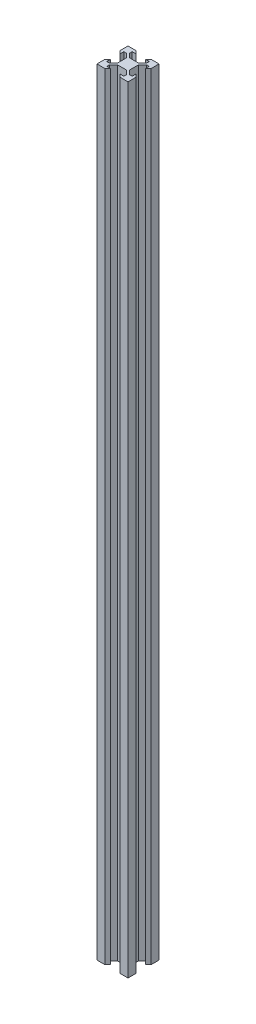
SolidWorks part; units mm, degrees
ref_plane "Front Plane" through (0, 0, 0) normal (0, 0, 1) x (1, 0, 0)
ref_plane "Top Plane" through (0, 0, 0) normal (0, 1, 0) x (1, 0, 0)
ref_plane "Right Plane" through (0, 0, 0) normal (1, 0, 0) x (0, 0, -1)
sketch "Sketch1" plane through (0, 0, 0) normal (0, 1, 0) x (1, 0, 0)
  line L0 (0, 93.8825) -> (0, -83.9719) construction
  line L1 (2.84, -3.9007) -> (-2.84, -3.9007)
  line L2 (3.9007, -2.84) -> (3.9007, 2.84)
  line L3 (2.84, 3.9007) -> (-2.84, 3.9007)
  line L4 (-3.9007, -2.84) -> (-3.9007, 2.84)
  line L7 (-194.997, 0) -> (154.5512, 0) construction
  line L8 (-2.84, -3.9007) -> (-5.4993, -6.56)
  line L9 (-5.4993, -6.56) -> (-5.4993, -8.2)
  line L10 (-5.4993, -8.2) -> (-3.1, -8.2)
  line L11 (-3.1, -8.2) -> (-4.9, -10)
  line L12 (-4.9, -10) -> (-10, -10)
  line L13 (-3.9007, -2.84) -> (-6.56, -5.4993)
  line L14 (-6.56, -5.4993) -> (-8.2, -5.4993)
  line L15 (-8.2, -5.4993) -> (-8.2, -3.1)
  line L16 (-8.2, -3.1) -> (-10, -4.9)
  line L17 (-10, -4.9) -> (-10, -10)
  line L18 (10, -4.9) -> (10, -10)
  line L19 (8.2, -3.1) -> (10, -4.9)
  line L20 (8.2, -5.4993) -> (8.2, -3.1)
  line L21 (6.56, -5.4993) -> (8.2, -5.4993)
  line L22 (3.9007, -2.84) -> (6.56, -5.4993)
  line L23 (4.9, -10) -> (10, -10)
  line L24 (3.1, -8.2) -> (4.9, -10)
  line L25 (5.4993, -8.2) -> (3.1, -8.2)
  line L26 (5.4993, -6.56) -> (5.4993, -8.2)
  line L27 (2.84, -3.9007) -> (5.4993, -6.56)
  line L28 (2.84, 3.9007) -> (5.4993, 6.56)
  line L29 (5.4993, 6.56) -> (5.4993, 8.2)
  line L30 (5.4993, 8.2) -> (3.1, 8.2)
  line L31 (3.1, 8.2) -> (4.9, 10)
  line L32 (4.9, 10) -> (10, 10)
  line L33 (3.9007, 2.84) -> (6.56, 5.4993)
  line L34 (6.56, 5.4993) -> (8.2, 5.4993)
  line L35 (8.2, 5.4993) -> (8.2, 3.1)
  line L36 (8.2, 3.1) -> (10, 4.9)
  line L37 (10, 4.9) -> (10, 10)
  line L38 (-10, 4.9) -> (-10, 10)
  line L39 (-8.2, 3.1) -> (-10, 4.9)
  line L40 (-8.2, 5.4993) -> (-8.2, 3.1)
  line L41 (-6.56, 5.4993) -> (-8.2, 5.4993)
  line L42 (-3.9007, 2.84) -> (-6.56, 5.4993)
  line L43 (-4.9, 10) -> (-10, 10)
  line L44 (-3.1, 8.2) -> (-4.9, 10)
  line L45 (-5.4993, 8.2) -> (-3.1, 8.2)
  line L46 (-5.4993, 6.56) -> (-5.4993, 8.2)
  line L47 (-2.84, 3.9007) -> (-5.4993, 6.56)
  point P0 (0, 0)
  point P4 (4.1697, 5.2303)
  dimension "D1" = 90
  dimension "D2" = 20
  dimension "D3" = 1.64
  dimension "D4" = 1.5
  dimension "D5" = 6.2
  dimension "D6" = 5.68
  dimension "D7" = 1.8
extrude "Boss-Extrude1" add sketch "Sketch1" along normal blind 500
